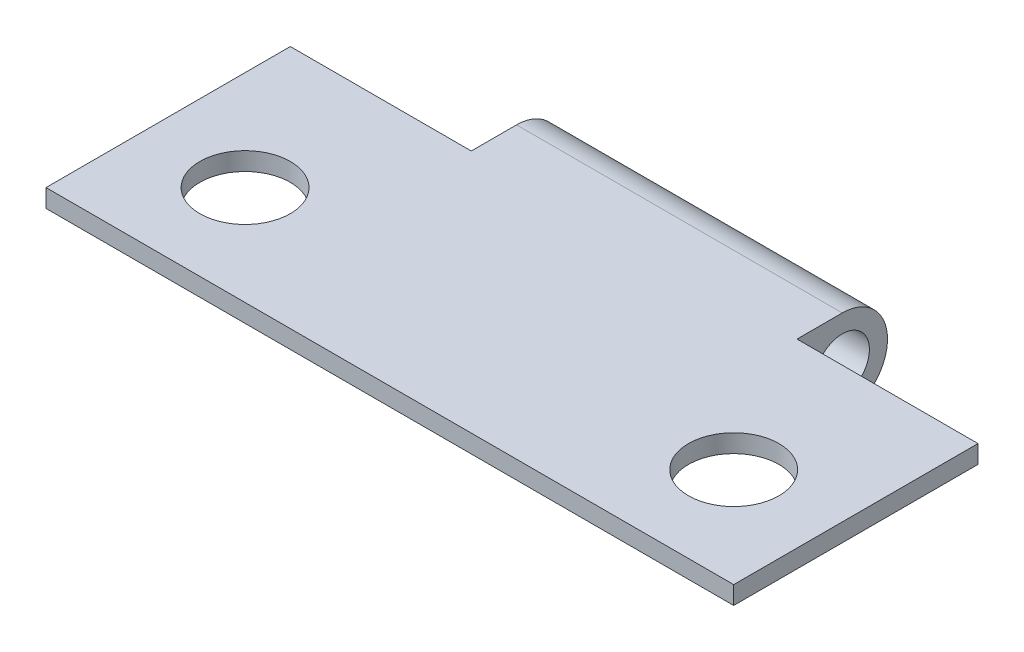
SolidWorks part; units mm, degrees
ref_plane "Front Plane" through (0, 0, 0) normal (0, 0, 1) x (1, 0, 0)
ref_plane "Top Plane" through (0, 0, 0) normal (0, 1, 0) x (1, 0, 0)
ref_plane "Right Plane" through (0, 0, 0) normal (1, 0, 0) x (0, 0, -1)
sketch "Sketch3" plane through (0, 0, 0) normal (1, 0, 0) x (0, 0, -1)
  line L0 (16, 1) -> (0, 1)
  line L1 (0, 0) -> (14, 0)
  line L2 (0, 0) -> (0, 1)
  arc A0 (16, 1) -> (14, 0) centre (16, -1.5) cw
  circle A1 centre (16, -1.5) radius 1.5
  dimension "D3" = 3
  dimension "D1" = 1
  dimension "D2" = 14
extrude "Boss-Extrude2" add sketch "Sketch3" along normal blind 38
sketch "Sketch4" plane through (0, 1, 0) normal (0, 1, 0) x (1, 0, 0)
  line L0 (19, 0) -> (19, 16) construction
  line L1 (38, 0) -> (0, 0) construction
  line L2 (38, 16) -> (0, 16) construction
  line L3 (38, 16) -> (38, 0) construction
  line L4 (38, 13.5) -> (28, 13.5)
  line L5 (38, 13.5) -> (38, 18.5)
  line L6 (38, 18.5) -> (28, 18.5)
  line L7 (28, 13.5) -> (28, 18.5)
  line L8 (10, 13.5) -> (10, 18.5)
  line L9 (0, 18.5) -> (10, 18.5)
  line L10 (0, 13.5) -> (0, 18.5)
  line L11 (0, 13.5) -> (10, 13.5)
  dimension "D1" = 2.5
  dimension "D2" = 5
  dimension "D3" = 10
extrude "Cut-Extrude1" cut sketch "Sketch4" against normal through all
sketch "Sketch5" plane through (0, 1, 0) normal (0, 1, 0) x (1, 0, 0)
  line L1 (0, 13.5) -> (0, 0) construction
  line L2 (38, 0) -> (0, 0) construction
  line L3 (19, 0) -> (19, 16) construction
  line L4 (28, 16) -> (10, 16) construction
  circle A0 centre (5.5, 5.5) radius 2.5
  circle A1 centre (32.5, 5.5) radius 2.5
  dimension "D1" = 5
  dimension "D2" = 5.5
  dimension "D3" = 5.5
extrude "Cut-Extrude2" cut sketch "Sketch5" against normal through all
